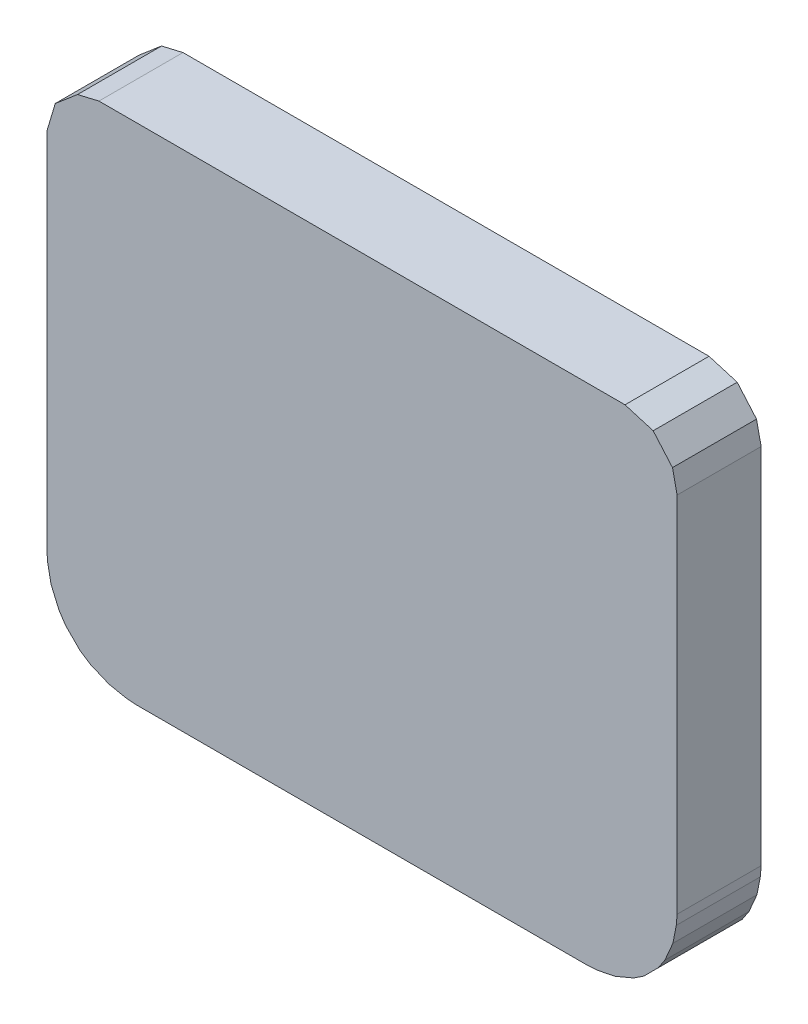
SolidWorks part; units mm, degrees
ref_plane "Front Plane" through (0, 0, 0) normal (0, 0, 1) x (1, 0, 0)
ref_plane "Top Plane" through (0, 0, 0) normal (0, 1, 0) x (1, 0, 0)
ref_plane "Right Plane" through (0, 0, 0) normal (1, 0, 0) x (0, 0, -1)
sketch "Model" plane through (0, 0, 0) normal (0, 0, 1) x (1, 0, 0)
  line L0 (-25.7537, -3.046) -> (-25.6445, -3.06)
  line L1 (-25.6445, -3.06) -> (-25.6132, -3.068)
  line L2 (-25.6132, -3.068) -> (-25.5228, -3.106)
  line L3 (-25.5228, -3.106) -> (-25.4948, -3.122)
  line L4 (-25.4948, -3.122) -> (-25.4171, -3.182)
  line L5 (-25.4171, -3.182) -> (-25.3942, -3.205)
  line L6 (-25.3942, -3.205) -> (-25.3346, -3.282)
  line L7 (-25.3346, -3.282) -> (-25.3185, -3.31)
  line L8 (-25.3185, -3.31) -> (-25.281, -3.401)
  line L9 (-25.281, -3.401) -> (-25.2726, -3.432)
  line L10 (-25.2726, -3.432) -> (-25.2582, -3.541)
  line L11 (-25.2582, -3.541) -> (-25.2577, -3.549)
  line L12 (-25.2577, -3.549) -> (-25.2577, -4.045)
  line L13 (-25.2577, -4.045) -> (-25.2349, -4.16)
  line L14 (-25.2349, -4.16) -> (-25.17, -4.257)
  line L15 (-25.17, -4.257) -> (-25.069, -4.325)
  line L16 (-25.069, -4.325) -> (-25.024, -4.379)
  line L17 (-25.024, -4.379) -> (-25.014, -4.428)
  line L18 (-25.014, -4.428) -> (-25.018, -6.466)
  line L19 (-25.018, -6.466) -> (-25.038, -6.533)
  line L20 (-25.038, -6.533) -> (-25.074, -6.569)
  line L21 (-25.074, -6.569) -> (-25.17, -6.633)
  line L22 (-25.17, -6.633) -> (-25.2349, -6.73)
  line L23 (-25.2349, -6.73) -> (-25.2577, -6.845)
  line L24 (-25.2577, -6.845) -> (-25.2577, -7.341)
  line L25 (-25.2577, -7.341) -> (-25.2582, -7.349)
  line L26 (-25.2582, -7.349) -> (-25.2726, -7.458)
  line L27 (-25.2726, -7.458) -> (-25.281, -7.49)
  line L28 (-25.281, -7.49) -> (-25.3184, -7.58)
  line L29 (-25.3184, -7.58) -> (-25.3346, -7.608)
  line L30 (-25.3346, -7.608) -> (-25.3942, -7.686)
  line L31 (-25.3942, -7.686) -> (-25.4171, -7.709)
  line L32 (-25.4171, -7.709) -> (-25.4947, -7.768)
  line L33 (-25.4947, -7.768) -> (-25.5228, -7.784)
  line L34 (-25.5228, -7.784) -> (-25.6132, -7.822)
  line L35 (-25.6132, -7.822) -> (-25.6445, -7.83)
  line L36 (-25.6445, -7.83) -> (-25.7537, -7.845)
  line L37 (-25.7537, -7.845) -> (-25.7618, -7.845)
  line L38 (-25.7618, -7.845) -> (-27.9536, -7.845)
  line L39 (-27.9536, -7.845) -> (-27.9617, -7.845)
  line L40 (-27.9617, -7.845) -> (-28.0709, -7.83)
  line L41 (-28.0709, -7.83) -> (-28.1022, -7.822)
  line L42 (-28.1022, -7.822) -> (-28.1926, -7.784)
  line L43 (-28.1926, -7.784) -> (-28.2207, -7.768)
  line L44 (-28.2207, -7.768) -> (-28.2983, -7.709)
  line L45 (-28.2983, -7.709) -> (-28.3212, -7.686)
  line L46 (-28.3212, -7.686) -> (-28.3808, -7.608)
  line L47 (-28.3808, -7.608) -> (-28.397, -7.58)
  line L48 (-28.397, -7.58) -> (-28.4344, -7.49)
  line L49 (-28.4344, -7.49) -> (-28.4428, -7.458)
  line L50 (-28.4428, -7.458) -> (-28.4572, -7.349)
  line L51 (-28.4572, -7.349) -> (-28.4577, -7.341)
  line L52 (-28.4577, -7.341) -> (-28.4577, -3.549)
  line L53 (-28.4577, -3.549) -> (-28.4572, -3.541)
  line L54 (-28.4572, -3.541) -> (-28.4428, -3.432)
  line L55 (-28.4428, -3.432) -> (-28.4344, -3.401)
  line L56 (-28.4344, -3.401) -> (-28.3969, -3.31)
  line L57 (-28.3969, -3.31) -> (-28.3808, -3.282)
  line L58 (-28.3808, -3.282) -> (-28.3212, -3.205)
  line L59 (-28.3212, -3.205) -> (-28.2983, -3.182)
  line L60 (-28.2983, -3.182) -> (-28.2206, -3.122)
  line L61 (-28.2206, -3.122) -> (-28.1926, -3.106)
  line L62 (-28.1926, -3.106) -> (-28.1022, -3.068)
  line L63 (-28.1022, -3.068) -> (-28.0709, -3.06)
  line L64 (-28.0709, -3.06) -> (-27.9617, -3.046)
  line L65 (-27.9617, -3.046) -> (-27.9536, -3.045)
  line L66 (-27.9536, -3.045) -> (-25.7618, -3.045)
  line L67 (-25.7618, -3.045) -> (-25.7537, -3.046)
  line L68 (0.067, -0.02) -> (0.113, -0.073)
  line L69 (0.113, -0.073) -> (0.124, -0.124)
  line L70 (0.124, -0.124) -> (0.124, -0.988)
  line L71 (0.124, -0.988) -> (0.122, -1.012)
  line L72 (0.122, -1.012) -> (0.114, -1.053)
  line L73 (0.114, -1.053) -> (0.095, -1.097)
  line L74 (0.095, -1.097) -> (0.079, -1.121)
  line L75 (0.079, -1.121) -> (0.045, -1.155)
  line L76 (0.045, -1.155) -> (0.021, -1.171)
  line L77 (0.021, -1.171) -> (-0.024, -1.19)
  line L78 (-0.024, -1.19) -> (-0.064, -1.198)
  line L79 (-0.064, -1.198) -> (-0.088, -1.2)
  line L80 (-0.088, -1.2) -> (-1.164, -1.2)
  line L81 (-1.164, -1.2) -> (-1.188, -1.198)
  line L82 (-1.188, -1.198) -> (-1.228, -1.19)
  line L83 (-1.228, -1.19) -> (-1.273, -1.171)
  line L84 (-1.273, -1.171) -> (-1.297, -1.155)
  line L85 (-1.297, -1.155) -> (-1.331, -1.121)
  line L86 (-1.331, -1.121) -> (-1.347, -1.097)
  line L87 (-1.347, -1.097) -> (-1.366, -1.053)
  line L88 (-1.366, -1.053) -> (-1.374, -1.012)
  line L89 (-1.374, -1.012) -> (-1.376, -0.988)
  line L90 (-1.376, -0.988) -> (-1.376, -0.124)
  line L91 (-1.376, -0.124) -> (-1.356, -0.057)
  line L92 (-1.356, -0.057) -> (-1.303, -0.012)
  line L93 (-1.303, -0.012) -> (-1.252, 0)
  line L94 (-1.252, 0) -> (0, 0)
  line L95 (0, 0) -> (0.067, -0.02)
extrude "Boss-Extrude1" add sketch "Model" along normal blind 0.2
delete or keep bodies "Body-Delete/Keep 1" type delete bodies bodies 101
